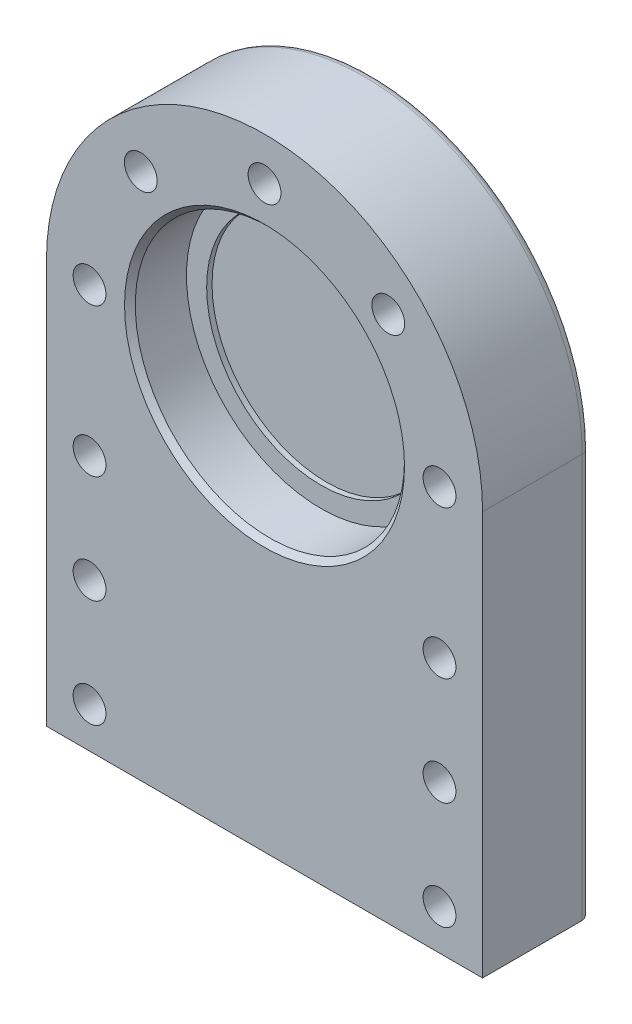
SolidWorks part; units mm, degrees
ref_plane "Front Plane" through (0, 0, 0) normal (0, 0, 1) x (1, 0, 0)
ref_plane "Top Plane" through (0, 0, 0) normal (0, 1, 0) x (1, 0, 0)
ref_plane "Right Plane" through (0, 0, 0) normal (1, 0, 0) x (0, 0, -1)
sketch "Sketch1" plane through (0, 0, 0) normal (0, 0, 1) x (1, 0, 0)
  line L0 (-81, 0) -> (-81, -150)
  line L1 (-81, -150) -> (81, -150)
  line L2 (81, -150) -> (81, 0)
  arc A0 (81, 0) -> (-81, 0) centre (0, 0) ccw
  dimension "D1" = 162
  dimension "D2" = 150
extrude "Boss-Extrude1" add sketch "Sketch1" along normal blind 40
sketch "Sketch2" plane through (0, 0, 40) normal (0, 0, 1) x (1, 0, 0)
  circle A0 centre (0, 0) radius 65 construction
  circle A1 centre (-65, 0) radius 6.1
  dimension "D1" = 130
  dimension "D2" = 12.2
extrude "Cut-Extrude1" cut sketch "Sketch2" against normal blind 40
pattern_circular "CirPattern1" count 5 over 180 about axis through (0, 0, 0) along (0, 0, 1) of "Cut-Extrude1"
sketch "Sketch3" plane through (0, 0, 40) normal (0, 0, 1) x (1, 0, 0)
  line L0 (-81, -150) -> (81, -150) construction
  line L1 (-81, 0) -> (-81, -150) construction
  circle A0 centre (-65, -135) radius 6.1
  circle A1 centre (-65, -95) radius 6.1
  circle A2 centre (-65, -55) radius 6.1
  point P10 (0, 0)
  point P11 (0, 0)
  point P12 (0, 0)
  point P13 (0, 0)
  dimension "D1" = 12.2
  dimension "D2" = 15
  dimension "D3" = 16
  dimension "D4" = 40
  dimension "D5" = 40
extrude "Cut-Extrude2" cut sketch "Sketch3" against normal blind 40
mirror "Mirror1" about plane through (0, 0, 0) normal (1, 0, 0) of "Cut-Extrude2"
sketch "Sketch5" plane through (0, 0, 40) normal (0, 0, 1) x (1, 0, 0)
  circle A0 centre (0, 0) radius 50
  dimension "D1" = 100
extrude "Cut-Extrude3" cut sketch "Sketch5" against normal blind 21
sketch "Sketch6" plane through (0, 0, 19) normal (0, 0, 1) x (1, 0, 0)
  circle A0 centre (0, 0) radius 42.5
  dimension "D1" = 85
extrude "Cut-Extrude4" cut sketch "Sketch6" against normal blind 2
chamfer "Chamfer1" distance 2 1 edges at (50, 0, 40)
fillet "Fillet1" radius 3 4 edges at (-81, -75, 0) (0, 81, 0) (81, -75, 0) (0, -150, 0)
